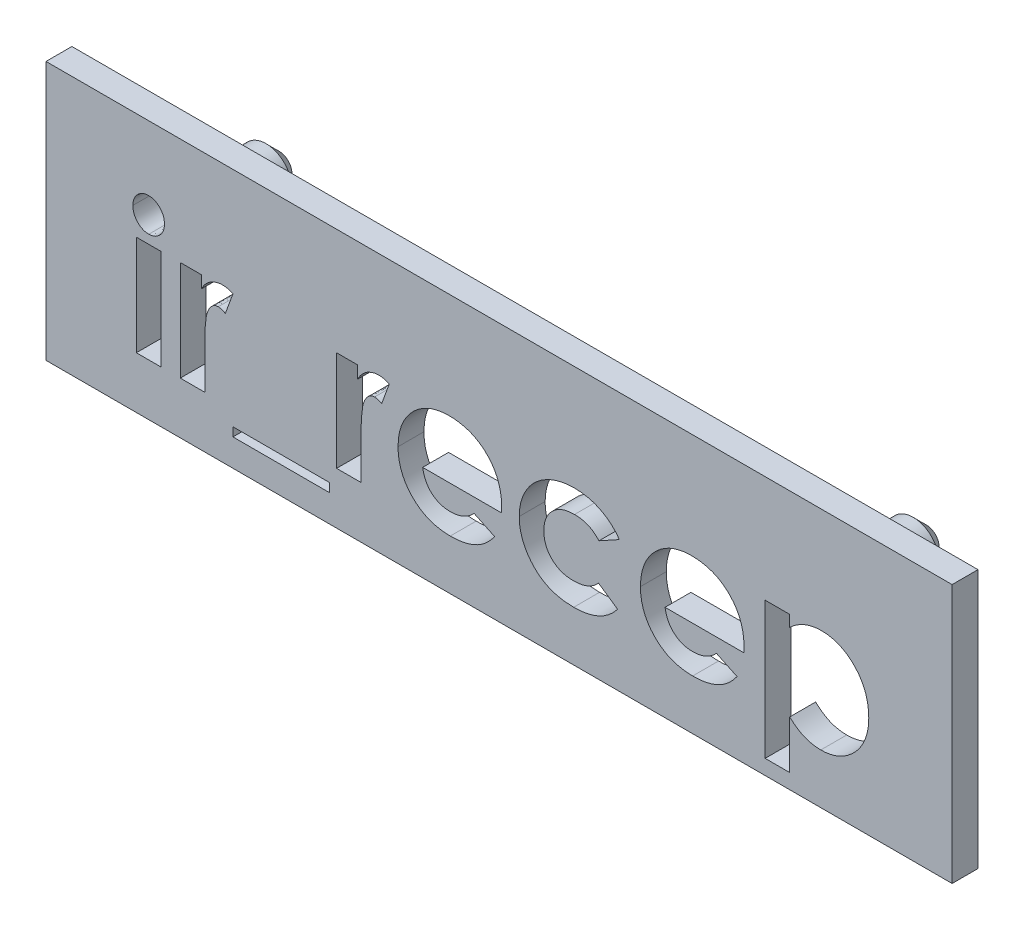
SolidWorks part; units mm, degrees
ref_plane "Plan de face" through (0, 0, 0) normal (0, 0, 1) x (1, 0, 0)
ref_plane "Plan de dessus" through (0, 0, 0) normal (0, 1, 0) x (1, 0, 0)
ref_plane "Plan de droite" through (0, 0, 0) normal (1, 0, 0) x (0, 0, -1)
sketch "Esquisse1" plane through (0, 0, 0) normal (0, 0, 1) x (1, 0, 0)
  line L1 (0, 0) -> (35, 0)
  line L2 (0, 0) -> (0, -10)
  line L3 (0, -10) -> (35, -10)
  line L4 (35, 0) -> (35, -10)
  dimension "D1" = 35
  dimension "D2" = 10
extrude "Boss.-Extru.1" add sketch "Esquisse1" along normal blind 1
sketch "Esquisse2" plane through (0, 0, 0) normal (0, 0, -1) x (-1, 0, 0)
  line L0 (-35, 0) -> (0, 0) construction
  line L1 (-35, -10) -> (-35, 0) construction
  line L2 (0, 0) -> (0, -10) construction
  circle A0 centre (-30, -3) radius 1
  circle A1 centre (-5, -3) radius 1
  dimension "D4" = 2
  dimension "D1" = 3
  dimension "D2" = 5
  dimension "D3" = 5
extrude "Boss.-Extru.2" add sketch "Esquisse2" along normal blind 3
chamfer "Chanfrein1" distance 0.5 angle 45 2 edges at (29, -3, -3) (4, -3, -3)
sketch "Esquisse3" plane through (0, 0, 1) normal (0, 0, 1) x (1, 0, 0)
  line L0 (2.5, -8) -> (32.5, -8) construction
  line L3 (0, -10) -> (35, -10) construction
  line L4 (0, 0) -> (0, -10) construction
  line L5 (35, -10) -> (35, 0) construction
  text T1 "<b>ir_recep</b>" font "Century Gothic" height in points 20
  point P12 (32.5, -8)
  dimension "D1" = 2
  dimension "D2" = 2.5
  dimension "D3" = 30
  dimension "D4" = 2.5
extrude "Enlèv. mat.-Extru.2" cut sketch "Esquisse3" against normal blind 1
